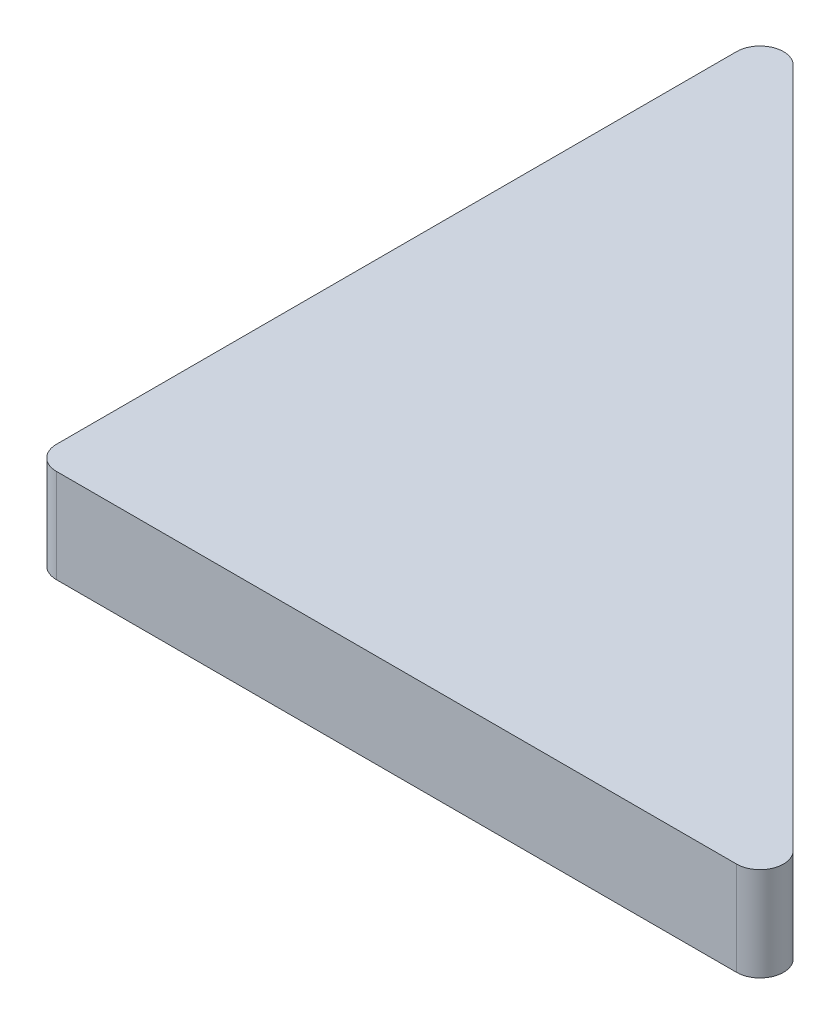
SolidWorks part; units mm, degrees
ref_plane "Front Plane" through (0, 0, 0) normal (0, 0, 1) x (1, 0, 0)
ref_plane "Top Plane" through (0, 0, 0) normal (0, 1, 0) x (1, 0, 0)
ref_plane "Right Plane" through (0, 0, 0) normal (1, 0, 0) x (0, 0, -1)
sketch "Sketch2" plane through (0, 0, 0) normal (0, 1, 0) x (1, 0, 0)
  line L0 (4.2678, 76.7629) -> (76.7629, 4.2678)
  line L1 (2.5, 0) -> (74.9951, 0)
  line L2 (0, 2.5) -> (0, 74.9951)
  line L5 (0, 0) -> (45.8475, 45.8475) construction
  arc A0 (2.5, 0) -> (0, 2.5) centre (2.5, 2.5) cw
  arc A1 (76.7629, 4.2678) -> (74.9951, 0) centre (74.9951, 2.5) cw
  arc A2 (4.2678, 76.7629) -> (0, 74.9951) centre (2.5, 74.9951) ccw
  point P3 (45.8475, 45.8475)
  point P5 (82.3541, 0)
  point P7 (2.5, 25)
  point P8 (25, 2.5)
  point P9 (2.5, 74.9951)
  point P10 (74.9951, 2.5)
  dimension "D2" = 2.5
  dimension "D1" = 45
  dimension "D3" = 45
  dimension "D4" = 25
  dimension "D5" = 0
  dimension "D6" = 2.5
  dimension "D7" = 49.9951
  dimension "D8" = 2.5
extrude "Boss-Extrude1" add sketch "Sketch2" along normal blind 10 contours L2 A2 L0 A1 L1 A0
sketch "Sketch3" plane through (0, 10, 0) normal (0, 1, 0) x (1, 0, 0)
  line L0 (2.5, 0) -> (74.9951, 0) construction
  line L1 (0, 2.5) -> (0, 74.9951) construction
  line L2 (0, 0) -> (78.6966, 78.6966) construction
  line L3 (-80.8215, 80.8215) -> (0, 0) construction
  point P0 (2.5, 75)
  point P1 (2.5, 25)
  point P6 (-78.6741, 82.9132)
  point P9 (25, 2.5)
  point P11 (75, 2.5)
  dimension "D1" = 25
  dimension "D2" = 50
  dimension "D3" = 2.5
  dimension "D4" = 0
  dimension "D5" = 45
  dimension "D6" = 90
  dimension "D7" = 19.4454
  dimension "D8" = 15.9099
  dimension "D9" = 51.2652
  dimension "D10" = 54.8008
